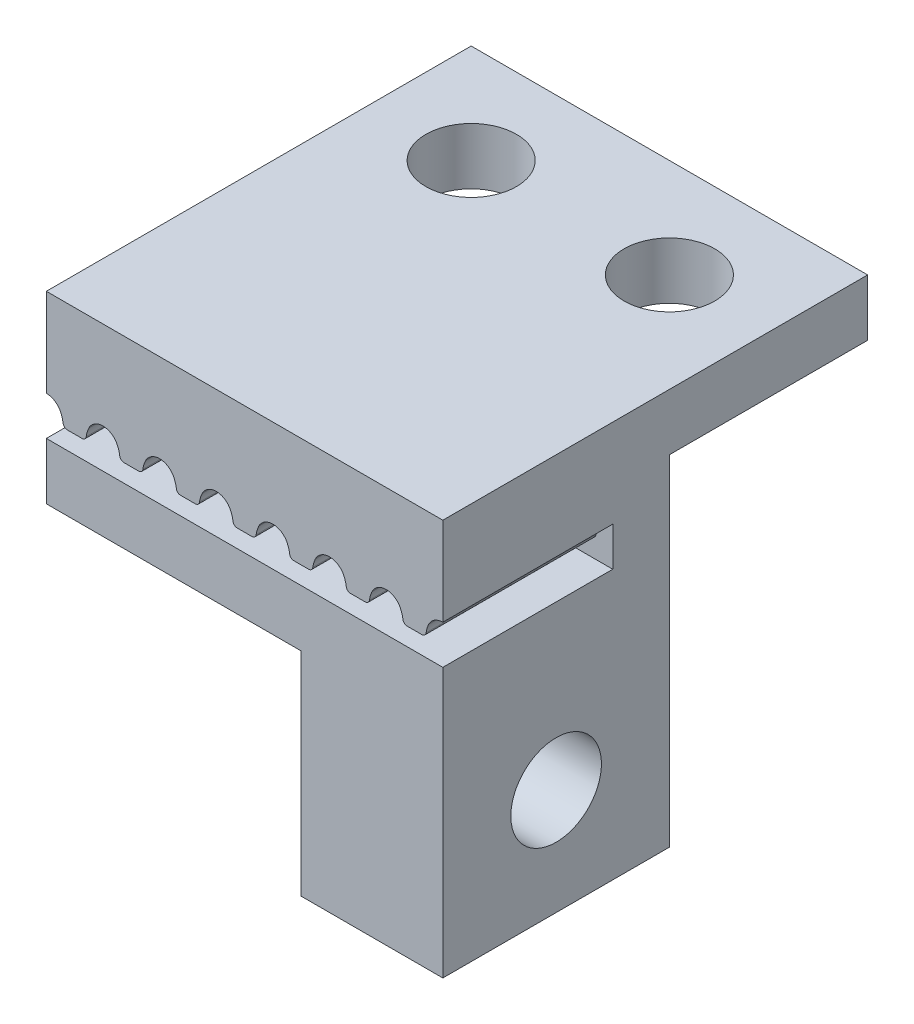
SolidWorks part; units mm, degrees
material "ABS"
ref_plane "Front Plane" through (0, 0, 0) normal (0, 0, 1) x (1, 0, 0)
ref_plane "Top Plane" through (0, 0, 0) normal (0, 1, 0) x (1, 0, 0)
ref_plane "Right Plane" through (0, 0, 0) normal (1, 0, 0) x (0, 0, -1)
sketch "Sketch3" plane through (0, 0, 0) normal (0, 0, 1) x (1, 0, 0)
  line L1 (0, -2) -> (14, -2)
  line L2 (0, -2) -> (0, 4.5)
  line L3 (0, 4.5) -> (14, 4.5)
  line L4 (14, -2) -> (14, 4.5)
  dimension "D1" = 14
  dimension "D2" = 6.5
  dimension "D3" = 2
extrude "Boss-Extrude2" add sketch "Sketch3" along normal blind 8
sketch "Sketch1" plane through (0, 0, 0) normal (0, 0, 1) x (1, 0, 0)
  line L4 (1, 0.63) -> (1, 1.38) construction
  line L5 (0.7402, 0.63) -> (1.2598, 0.63)
  line L6 (2, 1.38) -> (2, 0)
  line L9 (0, 1.38) -> (0, 0)
  line L10 (0, 0) -> (2, 0)
  arc A0 (1.2598, 0.63) -> (1.4085, 0.7604) centre (1.2598, 0.78) ccw
  arc A1 (1.4085, 0.7604) -> (1.5011, 1.0682) centre (2.4, 0.63) cw
  arc A2 (1.5011, 1.0682) -> (2, 1.38) centre (2, 0.825) cw
  arc A3 (0.4989, 1.0682) -> (0, 1.38) centre (0, 0.825) ccw
  arc A4 (0.5915, 0.7604) -> (0.4989, 1.0682) centre (-0.4, 0.63) ccw
  arc A5 (0.7402, 0.63) -> (0.5915, 0.7604) centre (0.7402, 0.78) cw
  dimension "D1" = 0.555
  dimension "D2" = 1
  dimension "D3" = 0.15
  dimension "D4" = 0.4
  dimension "D5" = 0.75
  dimension "D6" = 2
  dimension "D7" = 1.38
extrude "Cut-Extrude1" cut sketch "Sketch1" along normal blind 6 from offset 2
pattern_linear "LPattern2" count 7 spacing 2 along (1, 0, 0) of "Cut-Extrude1"
sketch "Sketch4" plane through (0, 4.5, 0) normal (0, 1, 0) x (-1, 0, 0)
  line L1 (-14, 0) -> (0, 0)
  line L2 (-14, 0) -> (-14, -7)
  line L3 (-14, -7) -> (0, -7)
  line L4 (0, 0) -> (0, -7)
  line L5 (-14, 0) -> (0, 0) construction
  line L6 (-14, 8) -> (-14, 0) construction
  line L7 (0, 8) -> (0, 0) construction
  line L8 (-14, -3.5) -> (0, -3.5) construction
  circle A0 centre (-10.5, -3.5) radius 1.6
  circle A1 centre (-3.5, -3.5) radius 1.6
  dimension "D5" = 3.2
  dimension "D1" = 3.5
  dimension "D2" = 7
  dimension "D3" = 7
  dimension "D4" = 3.5
extrude "Boss-Extrude3" add sketch "Sketch4" against normal blind 2
sketch "Sketch5" plane through (0, -2, 0) normal (0, -1, 0) x (1, 0, 0)
  line L0 (14, 8) -> (14, 0) construction
  line L1 (14, 8) -> (9, 8)
  line L2 (14, 8) -> (14, 0)
  line L3 (14, 0) -> (9, 0)
  line L4 (9, 8) -> (9, 0)
  line L5 (0, 0) -> (14, 0) construction
  line L6 (0, 8) -> (14, 8) construction
  dimension "D1" = 5
extrude "Boss-Extrude4" add sketch "Sketch5" along normal blind 7.5
sketch "Sketch6" plane through (9, 0, 0) normal (-1, 0, 0) x (0, 0, 1)
  line L0 (8, -9.5) -> (0, -9.5) construction
  line L2 (0, -9.5) -> (0, -2) construction
  circle A0 centre (4, -5.75) radius 1.6
  dimension "D3" = 3.2
  dimension "D1" = 3.75
  dimension "D2" = 4
extrude "Cut-Extrude2" cut sketch "Sketch6" against normal blind 7.5
